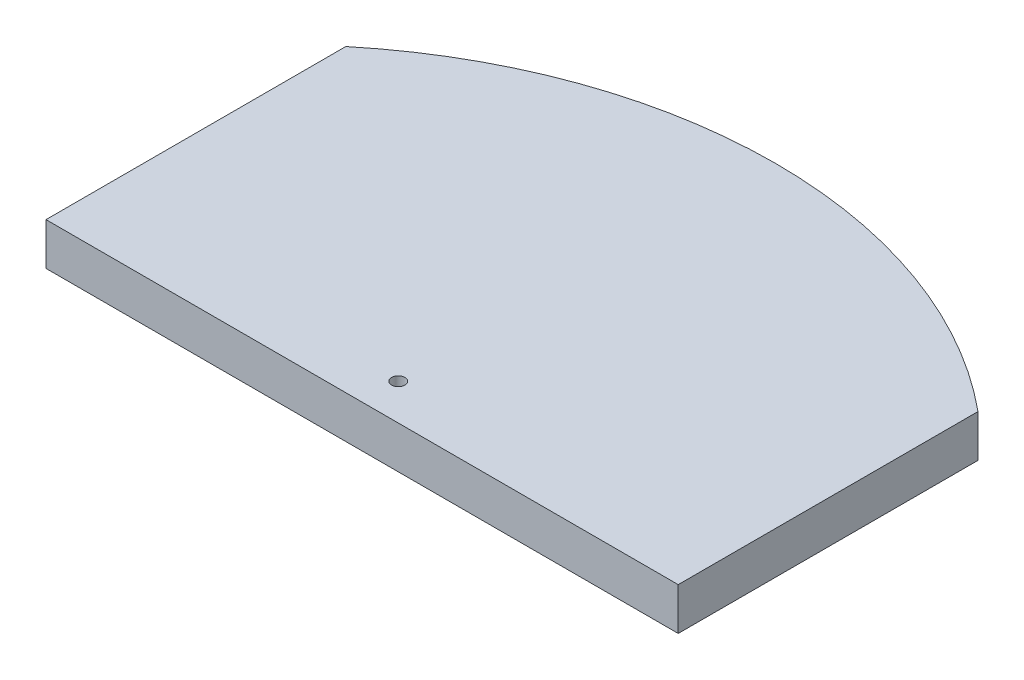
SolidWorks part; units mm, degrees
ref_plane "Front Plane" through (0, 0, 0) normal (0, 0, 1) x (1, 0, 0)
ref_plane "Top Plane" through (0, 0, 0) normal (0, 1, 0) x (1, 0, 0)
ref_plane "Right Plane" through (0, 0, 0) normal (1, 0, 0) x (0, 0, -1)
sketch "Sketch1" plane through (0, 0, 0) normal (0, 1, 0) x (1, 0, 0)
  line L0 (-47.45, -31.6854) -> (-47.45, -76.6854)
  line L1 (0, 0) -> (0, -76.6854) construction
  line L2 (47.45, -31.6854) -> (47.45, -76.6854)
  line L3 (-47.45, -76.6854) -> (47.45, -76.6854)
  arc A0 (-47.45, -31.6854) -> (47.45, -31.6854) centre (0, -89.1201) cw
  circle A1 centre (0, -71.2603) radius 1
  dimension "D3" = 74.5
  dimension "D4" = 2
  dimension "D1" = 94.9
  dimension "D2" = 45
extrude "Boss-Extrude1" add sketch "Sketch1" along normal blind 6.35
